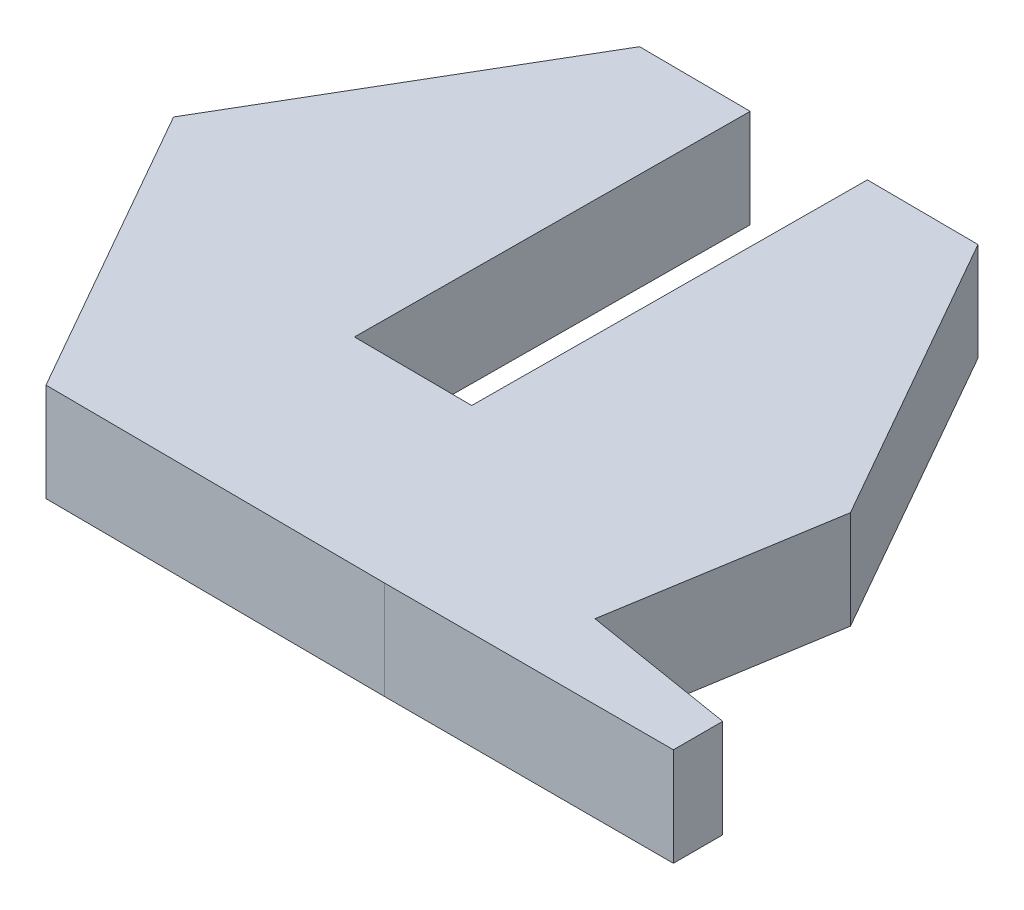
SolidWorks part; units mm, degrees
ref_plane "Front Plane" through (0, 0, 0) normal (0, 0, 1) x (1, 0, 0)
ref_plane "Top Plane" through (0, 0, 0) normal (0, 1, 0) x (1, 0, 0)
ref_plane "Right Plane" through (0, 0, 0) normal (1, 0, 0) x (0, 0, -1)
sketch "Sketch1" plane through (0, 0, 0) normal (0, 1, 0) x (1, 0, 0)
  line L10 (12.6941, -6.9341) -> (12.6941, -8.1889)
  line L12 (-3.314, -8.1347) -> (5.346, -8.1889)
  line L13 (12.6941, -8.1889) -> (5.346, -8.1889)
  line L14 (8.8103, -6.2992) -> (12.6941, -6.9341)
  line L15 (9.723, -0.7161) -> (5.4399, 6.8109)
  line L16 (-3.2202, 6.865) -> (-7.5972, -0.6077)
  line L17 (-7.5972, -0.6077) -> (-3.314, -8.1347)
  line L18 (9.723, -0.7161) -> (8.8103, -6.2992)
  line L19 (5.4399, 6.8109) -> (-3.2202, 6.865)
extrude "Boss-Extrude1" add sketch "Sketch1" along normal blind 2.5
sketch "Sketch2" plane through (0.0428, 0, -6.8446) normal (0.0063, 0, -1) x (-1, 0, -0.0063)
  line L0 (-5.3972, 0) -> (3.2631, 0) construction
  line L1 (-2.5672, 0) -> (0.4328, 0)
  line L2 (-2.5672, 0) -> (-2.5672, 2.5)
  line L3 (-2.5672, 2.5) -> (0.4328, 2.5)
  line L4 (0.4328, 0) -> (0.4328, 2.5)
  line L5 (-5.3972, 2.5) -> (3.2631, 2.5) construction
  line L6 (-5.3972, 2.5) -> (-5.3972, 0) construction
  dimension "D1" = 3
  dimension "D2" = 2.83
extrude "Cut-Extrude1" cut sketch "Sketch2" against normal blind 10
